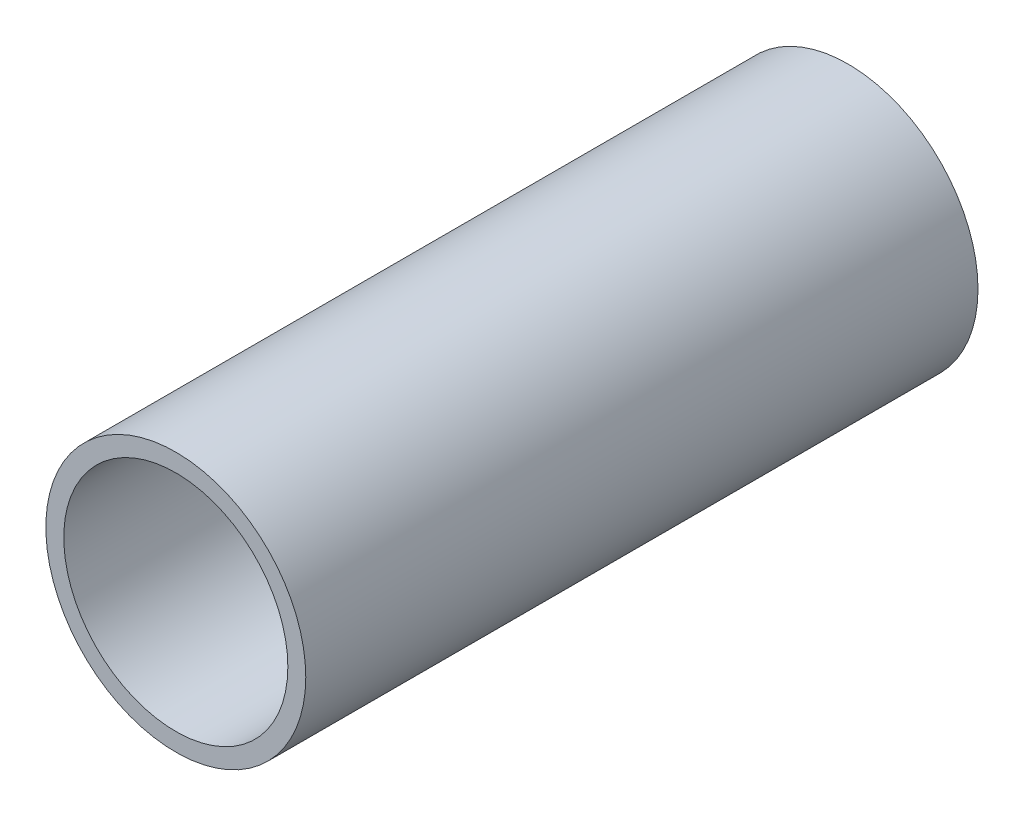
SolidWorks part; units mm, degrees
material "6061-T6 (SS)"
ref_plane "Front Plane" through (0, 0, 0) normal (0, 0, 1) x (1, 0, 0)
ref_plane "Top Plane" through (0, 0, 0) normal (0, 1, 0) x (1, 0, 0)
ref_plane "Right Plane" through (0, 0, 0) normal (1, 0, 0) x (0, 0, -1)
sketch "Sketch1" plane through (0, 0, 0) normal (0, 0, 1) x (1, 0, 0)
  circle A1 centre (0, 0) radius 14.5
  circle A2 centre (0, 0) radius 9.85
  dimension "D2" = 29
  dimension "D3" = 19.7
extrude "Boss-Extrude1" add sketch "Sketch1" along normal mid plane 18
sketch "Sketch2" plane through (0, 0, 0) normal (0, 0, 1) x (1, 0, 0)
  circle A0 centre (0, 0) radius 12.5
  circle A1 centre (0, 0) radius 14.5
  dimension "D1" = 25
  dimension "D2" = 29
extrude "Boss-Extrude2" add sketch "Sketch2" along normal mid plane 75
